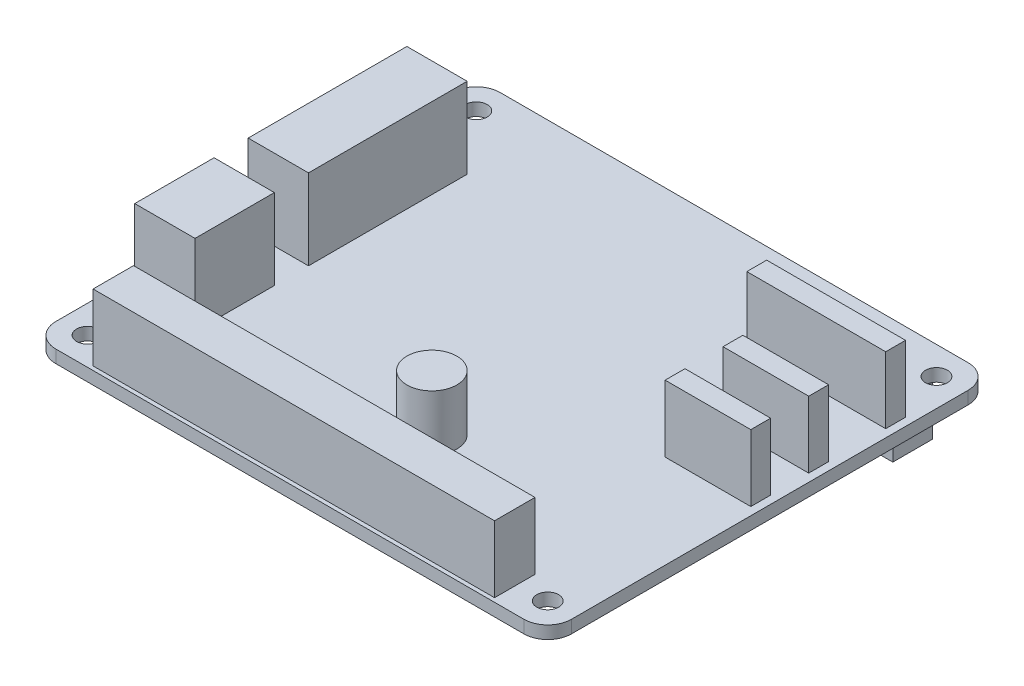
SolidWorks part; units mm, degrees
material "Plain Carbon Steel"
ref_plane "Front Plane" through (0, 0, 0) normal (0, 0, 1) x (1, 0, 0)
ref_plane "Top Plane" through (0, 0, 0) normal (0, 1, 0) x (1, 0, 0)
ref_plane "Right Plane" through (0, 0, 0) normal (1, 0, 0) x (0, 0, -1)
sketch "Sketch1" plane through (0, 0, 0) normal (0, 1, 0) x (1, 0, 0)
  line L0 (32.5, 0) -> (32.5, 56) construction
  line L1 (3, 0) -> (62, 0)
  line L2 (0, 3) -> (0, 53)
  line L3 (3, 56) -> (62, 56)
  line L4 (65, 3) -> (65, 53)
  line L5 (65, 28) -> (0, 28) construction
  circle A0 centre (3.5, 52.5) radius 1.375
  arc A1 (62, 56) -> (65, 53) centre (62, 53) cw
  arc A2 (62, 0) -> (65, 3) centre (62, 3) ccw
  arc A3 (3, 0) -> (0, 3) centre (3, 3) cw
  arc A4 (0, 53) -> (3, 56) centre (3, 53) cw
  circle A8 centre (61.5, 52.5) radius 1.375
  circle A9 centre (3.5, 3.5) radius 1.375
  circle A10 centre (61.5, 3.5) radius 1.375
  point P9 (65, 56)
  point P14 (0, 0)
  point P17 (0, 56)
  dimension "D3" = 2.75
  dimension "D6" = 3
  dimension "D4" = 58
  dimension "D5" = 49
  dimension "D1" = 65
  dimension "D2" = 56
extrude "Boss-Extrude1" add sketch "Sketch1" along normal blind 1.6
sketch "Sketch2" plane through (0, 1.6, 0) normal (0, 1, 0) x (1, 0, 0)
  line L0 (62, 56) -> (3, 56) construction
  line L1 (2.25, 45) -> (9.85, 45)
  line L2 (2.25, 45) -> (2.25, 25)
  line L3 (2.25, 25) -> (9.85, 25)
  line L4 (9.85, 45) -> (9.85, 25)
  line L5 (2.25, 20.7) -> (9.85, 20.7)
  line L6 (2.25, 20.7) -> (2.25, 10.7)
  line L7 (2.25, 10.7) -> (9.85, 10.7)
  line L8 (9.85, 20.7) -> (9.85, 10.7)
  line L9 (0, 53) -> (0, 3) construction
  point P10 (2.25, 35)
  dimension "D1" = 7.6
  dimension "D2" = 10
  dimension "D3" = 20
  dimension "D4" = 11
  dimension "D5" = 2.25
  dimension "D6" = 4.3
extrude "Boss-Extrude2" add sketch "Sketch2" along normal blind 10.15 contours L4 L1 L2 L3 | L8 L5 L6 L7
sketch "Sketch3" plane through (0, 1.6, 0) normal (0, 1, 0) x (1, 0, 0)
  line L0 (3, 0) -> (62, 0) construction
  line L1 (7.2, 5.6) -> (57.8, 5.6)
  line L2 (7.2, 5.6) -> (7.2, 0.5)
  line L3 (7.2, 0.5) -> (57.8, 0.5)
  line L4 (57.8, 5.6) -> (57.8, 0.5)
  point P6 (32.5, 0.5)
  point P7 (32.5, 0)
  dimension "D1" = 50.6
  dimension "D2" = 5.1
  dimension "D3" = 0.5
extrude "Boss-Extrude3" add sketch "Sketch3" along normal blind 8.4
sketch "Sketch4" plane through (0, 1.6, 0) normal (0, 1, 0) x (1, 0, 0)
  line L0 (36.05, 0) -> (36.05, 17.5) construction
  line L1 (3, 0) -> (62, 0) construction
  line L2 (32.9, 14.35) -> (65, 14.35) construction
  line L3 (65, 3) -> (65, 53) construction
  circle A0 centre (36.05, 14.35) radius 3.15
  dimension "D2" = 6.3
  dimension "D1" = 17.5
  dimension "D3" = 32.1
extrude "Boss-Extrude4" add sketch "Sketch4" along normal blind 7
sketch "Sketch5" plane through (0, 1.6, 0) normal (0, 1, 0) x (1, 0, 0)
  line L0 (65, 3) -> (65, 53) construction
  line L1 (46.5, 46.1) -> (64, 46.1)
  line L2 (46.5, 46.1) -> (46.5, 43.6)
  line L3 (46.5, 43.6) -> (64, 43.6)
  line L4 (64, 46.1) -> (64, 43.6)
  line L5 (64, 36.4) -> (53.2, 36.4)
  line L6 (64, 36.4) -> (64, 33.9)
  line L7 (64, 33.9) -> (53.2, 33.9)
  line L8 (53.2, 36.4) -> (53.2, 33.9)
  line L9 (64, 29.1) -> (53.2, 29.1)
  line L10 (64, 29.1) -> (64, 26.6)
  line L11 (64, 26.6) -> (53.2, 26.6)
  line L12 (53.2, 29.1) -> (53.2, 26.6)
  line L13 (62, 56) -> (3, 56) construction
  dimension "D1" = 1
  dimension "D2" = 2.5
  dimension "D3" = 12.4
  dimension "D4" = 7.2
  dimension "D5" = 4.8
  dimension "D6" = 17.5
  dimension "D7" = 10.8
extrude "Boss-Extrude5" add sketch "Sketch5" along normal blind 8.4
sketch "Sketch6" plane through (0, 0, 0) normal (0, -1, 0) x (1, 0, 0)
  line L0 (32.5, -56) -> (32.5, 0) construction
  line L1 (62, -56) -> (3, -56) construction
  line L2 (3, 0) -> (62, 0) construction
  line L4 (58.5, -50) -> (6.5, -50)
  line L5 (58.5, -50) -> (58.5, -55)
  line L6 (58.5, -55) -> (6.5, -55)
  line L7 (6.5, -50) -> (6.5, -55)
  line L8 (58.5, -50) -> (6.5, -55) construction
  line L9 (58.5, -55) -> (6.5, -50) construction
  point P6 (32.5, -52.5)
  dimension "D1" = 1
  dimension "D2" = 5
  dimension "D3" = 52
extrude "Boss-Extrude6" add sketch "Sketch6" along normal blind 8
